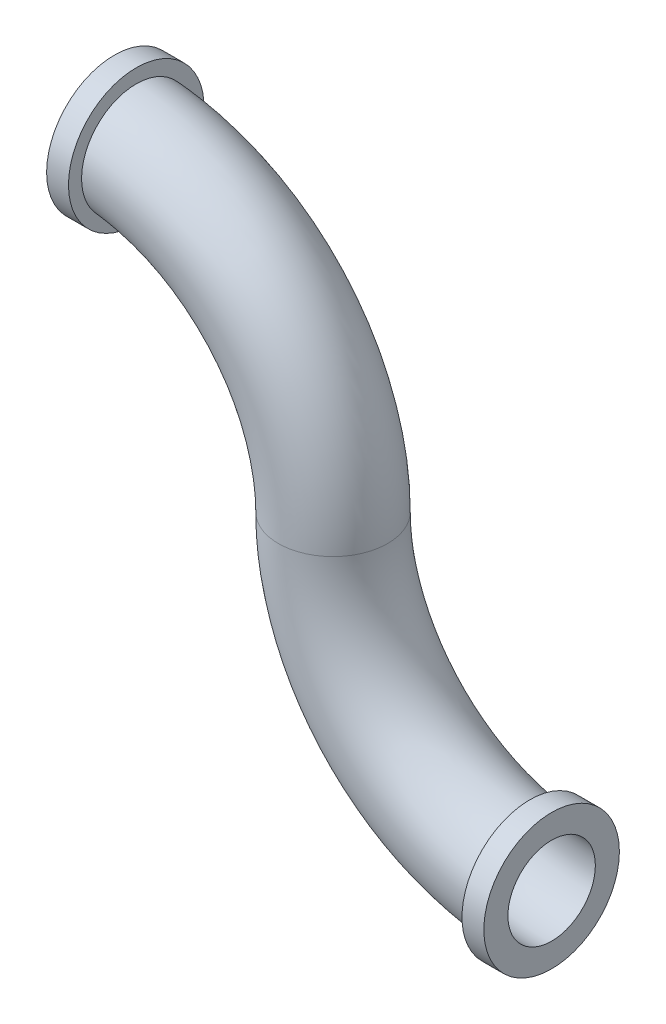
SolidWorks part; units mm, degrees
ref_plane "Ön Düzlem" through (0, 0, 0) normal (0, 0, 1) x (1, 0, 0)
ref_plane "Üst Düzlem" through (0, 0, 0) normal (0, 1, 0) x (1, 0, 0)
ref_plane "Sağ Düzlem" through (0, 0, 0) normal (1, 0, 0) x (0, 0, -1)
sketch "Çizim1" plane through (0, 0, 0) normal (0, 0, 1) x (1, 0, 0)
  arc A0 (0, 0) -> (1, -1) centre (1, 0) ccw
  arc A1 (0, 0) -> (-1, 1) centre (-1, 0) ccw
ref_plane "Düzlem1" through (1, 0, 0) normal (1, 0, 0) x (0, 0, -1)
sketch "Çizim3" plane through (1, 0, 0) normal (1, 0, 0) x (0, 0, -1)
  circle A0 centre (0, -1) radius 0.2
sketch "Çizim5" plane through (0, 0, 0) normal (0, 0, 1) x (1, 0, 0)
  line L0 (1, -1) -> (0.9, -1)
sweep "Süpür-İnce3" add profiles "Çizim3" path "Çizim1" parameters "D1"=0.05
sketch3d "3B Çizim1"
  circle A0 centre (-1, 1, 0) radius 0.2 construction
  point P0 (-1, 1, 0)
  point P4 (-0.8, 1, 0)
sketch "Çizim7" plane through (0, 0, 0) normal (0, 0, 1) x (1, 0, 0)
  line L0 (-1, 1) -> (-0.9, 1)
ref_plane "Düzlem3" through (-1, 0, 0) normal (-1, 0, 0) x (0, 0, 1)
sketch "Çizim8" plane through (-1, 0, 0) normal (-1, 0, 0) x (0, 0, 1)
  circle A0 centre (0, 1) radius 0.21
sweep "Süpür-İnce5" add profiles "Çizim8" path "Çizim7" parameters "D1"=0.1
sketch "Çizim9" plane through (1, 0, 0) normal (1, 0, 0) x (0, 0, -1)
  circle A0 centre (0, -1) radius 0.21
sweep "Süpür-İnce6" add profiles "Çizim9" path "Çizim5" parameters "D1"=0.1
